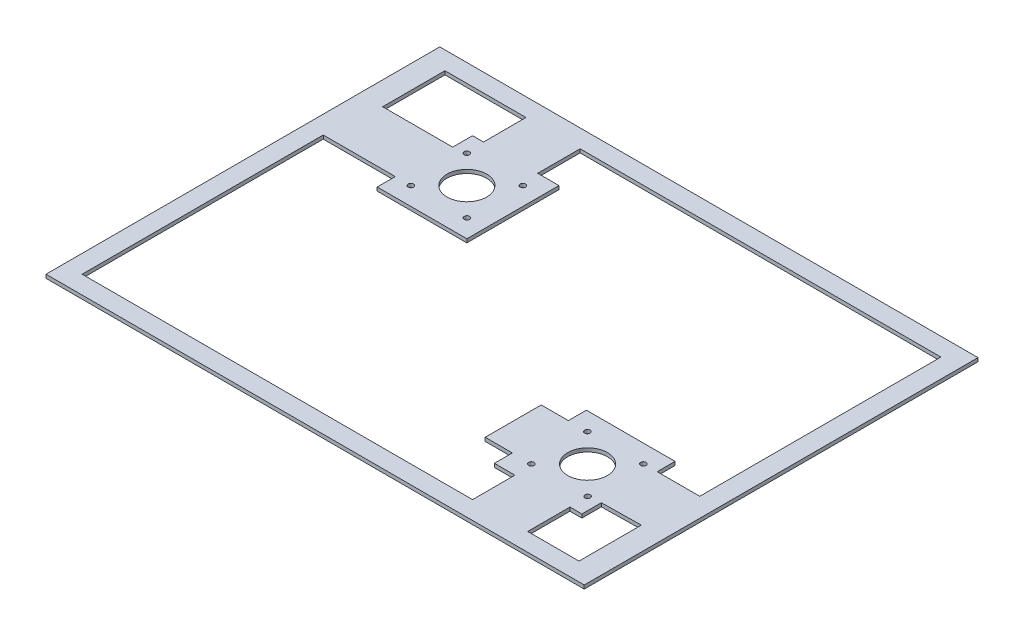
SolidWorks part; units mm, degrees
ref_plane "Front Plane" through (0, 0, 0) normal (0, 0, 1) x (1, 0, 0)
ref_plane "Top Plane" through (0, 0, 0) normal (0, 1, 0) x (1, 0, 0)
ref_plane "Right Plane" through (0, 0, 0) normal (1, 0, 0) x (0, 0, -1)
sketch "Sketch1" plane through (0, 0, 0) normal (1, 0, 0) x (0, 0, -1)
  line L0 (-26.6783, 0) -> (191.3217, 0)
  line L1 (119.9, 0) -> (-119.9, 0) construction
  line L2 (-26.6783, 0) -> (-26.6783, 2)
  line L3 (191.3217, 0) -> (191.3217, 2)
  line L4 (191.3217, 2) -> (-26.6783, 2)
  dimension "D1" = 218
  dimension "D2" = 2
extrude "Boss-Extrude1" add sketch "Sketch1" along normal blind 298 contours L4 L2 L0 L3
sketch "Sketch2" plane through (0, 2, 0) normal (0, 1, 0) x (1, 0, 0)
  line L0 (0, -1.1) -> (0, 1.1) construction
  line L5 (298, 191.3217) -> (0, 191.3217) construction
  line L6 (12.8876, 181.3217) -> (57.7212, 181.3217)
  line L7 (128.5445, 82.3217) -> (183.6204, 82.3217) construction
  line L18 (74, 132.3217) -> (85, 132.3217) construction
  line L20 (149, 244.2227) -> (149, 181.3217) construction
  line L23 (12.8876, 181.3217) -> (12.8876, 159.517)
  line L24 (298, -26.6783) -> (0, -26.6783) construction
  line L27 (85, 132.3217) -> (-63.8787, 132.3217) construction
  line L28 (149, -16.6783) -> (104.4712, -16.6783)
  line L29 (99.5, 106.8217) -> (99.5, 157.8217)
  line L30 (101.2006, 181.3217) -> (149, 181.3217)
  line L31 (51.6521, 157.8217) -> (57.7212, 157.8217)
  line L32 (104.4712, -16.6783) -> (10, -16.6783)
  line L34 (99.5, 106.8217) -> (49.8733, 106.8217)
  line L35 (10, -16.6783) -> (10, 89.9418)
  line L36 (57.7212, 181.3217) -> (57.7212, 157.8217)
  line L37 (99.5, 157.8217) -> (87.7212, 157.8217)
  line L39 (101.2006, 181.3217) -> (87.7212, 181.3217)
  line L40 (87.7212, 157.8217) -> (87.7212, 181.3217)
  line L42 (10, 89.9418) -> (10, 116.8217)
  line L43 (10, 116.8217) -> (49.8733, 116.8217)
  line L44 (49.8733, 106.8217) -> (49.8733, 116.8217)
  line L46 (12.8876, 159.517) -> (12.8876, 146.8217)
  line L47 (12.8876, 146.8217) -> (51.6521, 146.8217)
  line L48 (51.6521, 157.8217) -> (51.6521, 146.8217)
  line L49 (287.4591, 47.8217) -> (287.4591, 181.3217)
  line L50 (287.4591, 181.3217) -> (149, 181.3217)
  line L51 (226.1545, -16.6783) -> (149, -16.6783)
  line L52 (149, -16.6783) -> (149, -99.356) construction
  line L62 (214.9875, 235.2083) -> (214.9875, 57.7194) construction
  line L63 (287.4591, 47.8217) -> (263.8762, 47.8217)
  line L64 (285.1124, -16.6783) -> (285.1124, 5.1264)
  line L65 (285.1124, 5.1264) -> (285.1124, 17.8217)
  line L66 (285.1124, 17.8217) -> (263.3054, 17.4886)
  line L67 (263.3054, 6.7194) -> (263.3054, 17.4886)
  line L68 (263.3054, 6.7194) -> (256.6954, 6.7194)
  line L69 (256.6954, -16.6783) -> (256.6954, 6.7194)
  line L70 (285.1124, -16.6783) -> (256.6954, -16.6783)
  line L71 (214.7904, 57.7194) -> (214.7904, 47.7194)
  line L72 (214.7904, 57.7194) -> (263.8762, 57.7194)
  line L73 (214.7904, 6.7771) -> (226.1545, 6.7771)
  line L75 (226.1545, 6.7771) -> (226.1545, -16.6783)
  line L76 (263.8762, 57.7194) -> (263.8762, 47.8217)
  line L77 (214.7904, 16.7194) -> (214.7904, 6.7771)
  line L78 (214.7904, 47.7194) -> (199.7626, 47.7194)
  line L80 (214.7904, 16.7194) -> (199.7626, 16.7194)
  line L81 (199.7626, 47.7194) -> (199.7626, 16.7194)
  line L82 (214.9875, 6.7771) -> (214.9875, -106.0424) construction
  circle A0 centre (74, 132.3217) radius 11
  circle A4 centre (89.5, 116.8217) radius 1.5
  circle A5 centre (58.5, 116.8217) radius 1.5
  circle A6 centre (89.5, 147.8217) radius 1.5
  circle A7 centre (58.5, 147.8217) radius 1.5
  circle A13 centre (256.3313, 47.7194) radius 1.5
  circle A14 centre (256.4575, 16.7194) radius 1.5
  circle A15 centre (225.3313, 16.7194) radius 1.5
  circle A16 centre (225.3313, 47.7194) radius 1.5
  circle A17 centre (240.9575, 32.2194) radius 11
  point P52 (57.7212, 169.5717)
  dimension "D9" = 22
  dimension "D10" = 3
  dimension "D11" = 3
  dimension "D2" = 50
  dimension "D3" = 150
  dimension "D4" = 109
  dimension "D5" = 10
  dimension "D6" = 10
  dimension "D7" = 30
  dimension "D8" = 31
  dimension "D12" = 31
  dimension "D13" = 15.5
  dimension "D14" = 15.5
  dimension "D15" = 149
  dimension "D16" = 30
  dimension "D17" = 10
  dimension "D18" = 10
  dimension "D19" = 10
  dimension "D20" = 10
  dimension "D21" = 10
  dimension "D22" = 10
  dimension "D23" = 10
extrude "Cut-Extrude1" cut sketch "Sketch2" against normal blind 10
